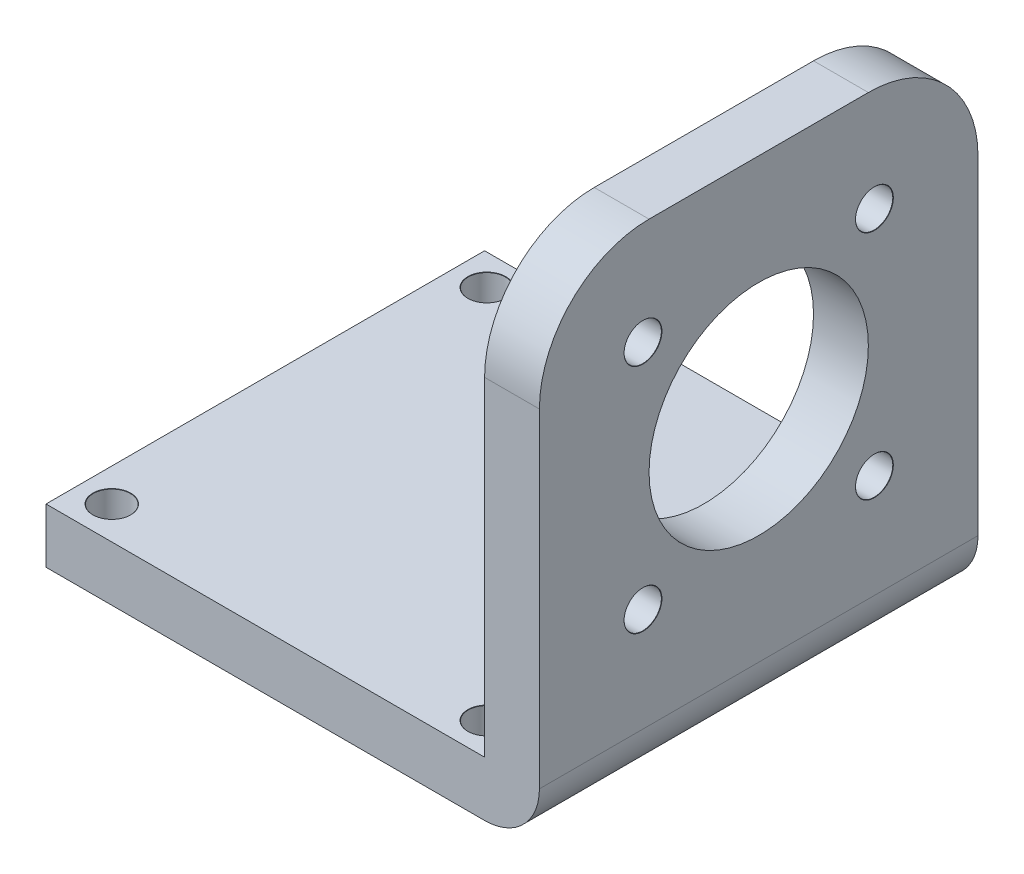
SolidWorks part; units mm, degrees
ref_plane "Front Plane" through (0, 0, 0) normal (0, 0, 1) x (1, 0, 0)
ref_plane "Top Plane" through (0, 0, 0) normal (0, 1, 0) x (1, 0, 0)
ref_plane "Right Plane" through (0, 0, 0) normal (1, 0, 0) x (0, 0, -1)
sketch "Sketch1" plane through (0, 0, 0) normal (0, 1, 0) x (1, 0, 0)
  line L1 (20, -20) -> (-20, -20)
  line L2 (20, -20) -> (20, 20)
  line L3 (20, 20) -> (-20, 20)
  line L4 (-20, -20) -> (-20, 20)
  line L5 (20, -20) -> (-20, 20) construction
  line L6 (20, 20) -> (-20, -20) construction
  point P0 (0, 0)
  dimension "D1" = 40
  dimension "D2" = 40
extrude "Boss-Extrude1" add sketch "Sketch1" along normal blind 5
sketch "Sketch2" plane through (0, 0, 0) normal (1, 0, 0) x (0, 0, -1)
  line L0 (-20, 0) -> (20, 0) construction
  line L1 (20, 0) -> (-20, 0)
  line L2 (20, 0) -> (20, 45)
  line L3 (20, 45) -> (-20, 45)
  line L4 (-20, 0) -> (-20, 45)
  line L5 (20, 0) -> (-20, 45) construction
  line L6 (20, 45) -> (-20, 0) construction
  point P0 (0, 22.5)
  dimension "D1" = 40
  dimension "D2" = 45
extrude "Boss-Extrude2" add sketch "Sketch2" along normal blind 5 from surface at 20 starting at face at (20, 2.5, 0)
fillet "Fillet1" radius 10 1 edges at (22.5, 45, 20)
fillet "Fillet2" radius 10 1 edges at (22.5, 45, -20)
fillet "Fillet3" radius 5 1 edges at (25, 0, 0)
sketch "Sketch3" plane through (20, 0, 0) normal (-1, 0, 0) x (0, 0, 1)
  line L0 (20, 5) -> (-20, 5) construction
  line L2 (11, 14) -> (-11, 14) construction
  line L3 (11, 14) -> (11, 36) construction
  line L4 (11, 36) -> (-11, 36) construction
  line L5 (-11, 14) -> (-11, 36) construction
  line L6 (11, 14) -> (-11, 36) construction
  line L7 (11, 36) -> (-11, 14) construction
  circle A0 centre (0, 25) radius 10
  dimension "D1" = 20
  dimension "D2" = 20
  dimension "D3" = 22
  dimension "D4" = 22
extrude "Cut-Extrude1" cut sketch "Sketch3" against normal blind 5
sketch "Sketch4" plane through (25, 0, 0) normal (1, 0, 0) x (0, 0, -1)
  line L0 (-10.5535, 35.5535) -> (0, 25) construction
  line L2 (0, 25) -> (-17.1114, 25) construction
  line L3 (-10.5535, 35.5535) -> (-10.5535, 25) construction
  point P0 (-10.5535, 35.5535)
  point P17 (-10.422, 35.2972)
  point P18 (-9.8403, 35.782)
  point P19 (-11.2806, 36.2806)
  point P20 (-10.5535, 35.5535)
  dimension "D1" = 45
  dimension "D2" = 25
hole_wizard "M3 Clearance Hole1" positions "Sketch4" profile "Sketch5" hole size "M3" standard "ISO" end condition through all
sketch "Sketch5" plane through (25, 35.5535, 10.5535) normal (0, 1, 0) x (0, 0, -1)
  line L0 (0, 0) -> (0, 45)
  line L1 (0, 45) -> (1.7, 45)
  line L2 (1.7, 45) -> (1.7, 0.025)
  line L3 (1.7, 0.025) -> (1.725, 0)
  line L5 (1.725, 0) -> (0, 0)
  line L6 (-1.7, 0.025) -> (-1.725, 0) construction
  line L11 (0, -6.35) -> (0, 107.95) construction
  dimension "Thru Hole Dia." = 3.4
  dimension "Thru Hole Depth" = 45
  dimension "Near C'Sink Dia." = 3.45
  dimension "Near C'Sink Angle" = 90
pattern_circular "CirPattern1" count 4 over 360 about axis through (0, 25, 0) along (1, 0, 0) of "M3 Clearance Hole1"
sketch "Sketch8" plane through (0, 5, 0) normal (0, 1, 0) x (1, 0, 0)
  circle A0 centre (0, 0) radius 7.5 construction
  dimension "D1" = 15
hole_wizard "M3 Clearance Hole2" positions "Sketch6" profile "Sketch7" hole size "M3" standard "ISO" end condition through all
sketch "Sketch6" plane through (0, 5, 0) normal (0, 1, 0) x (1, 0, 0)
  line L0 (0, 0) -> (0, -20) construction
  line L2 (-20, -20) -> (20, -20) construction
  line L3 (0, 0) -> (-20, 0) construction
  line L4 (-20, 20) -> (-20, -20) construction
  line L6 (0, 0) -> (-20, -20) construction
  point P0 (-17, -17)
  point P21 (-10.0176, -10.0176)
  point P22 (0, 0)
  dimension "D1" = 17
sketch "Sketch7" plane through (-17, 5, 17) normal (1, 0, 0) x (0, 0, 1)
  line L0 (0, 0) -> (0, 5)
  line L1 (0, 5) -> (1.7, 5)
  line L2 (1.7, 5) -> (1.7, 0.025)
  line L3 (1.7, 0.025) -> (1.725, 0)
  line L5 (1.725, 0) -> (0, 0)
  line L6 (-1.7, 0.025) -> (-1.725, 0) construction
  line L11 (0, -6.35) -> (0, 107.95) construction
  dimension "Thru Hole Dia." = 3.4
  dimension "Thru Hole Depth" = 5
  dimension "Near C'Sink Dia." = 3.45
  dimension "Near C'Sink Angle" = 90
pattern_circular "CirPattern2" count 4 over 360 about axis through (0.0999, 0, -0.0999) along (0, 1, 0) of "M3 Clearance Hole2"
